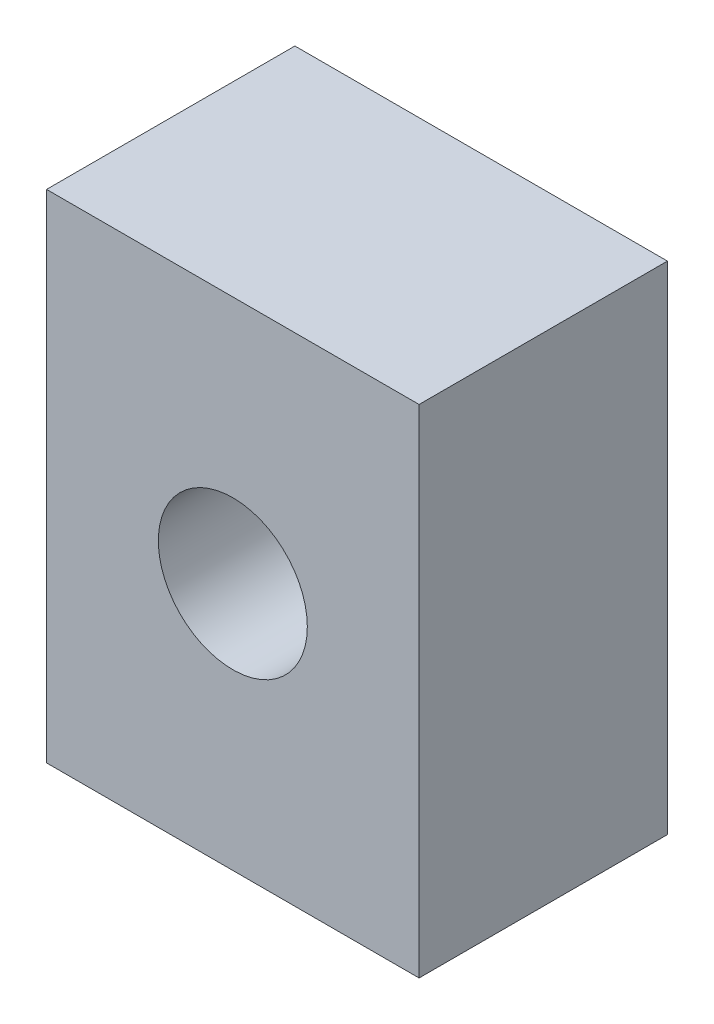
SolidWorks part; units mm, degrees
material "PET"
ref_plane "Front Plane" through (0, 0, 0) normal (0, 0, 1) x (1, 0, 0)
ref_plane "Top Plane" through (0, 0, 0) normal (0, 1, 0) x (1, 0, 0)
ref_plane "Right Plane" through (0, 0, 0) normal (1, 0, 0) x (0, 0, -1)
sketch "Sketch1" plane through (0, 0, 0) normal (0, 0, 1) x (1, 0, 0)
  line L1 (0, 0) -> (30, 0)
  line L2 (0, 0) -> (0, 40)
  line L3 (0, 40) -> (30, 40)
  line L4 (30, 0) -> (30, 40)
  dimension "D1" = 40
  dimension "D2" = 30
extrude "Boss-Extrude1" add sketch "Sketch1" along normal blind 20
sketch "Sketch2" plane through (0, 0, 20) normal (0, 0, 1) x (1, 0, 0)
  line L0 (0, 0) -> (30, 0) construction
  circle A0 centre (15, 20) radius 6
  point P4 (15, 0)
  dimension "D2" = 12
  dimension "D1" = 20
extrude "Cut-Extrude1" cut sketch "Sketch2" against normal blind 12
